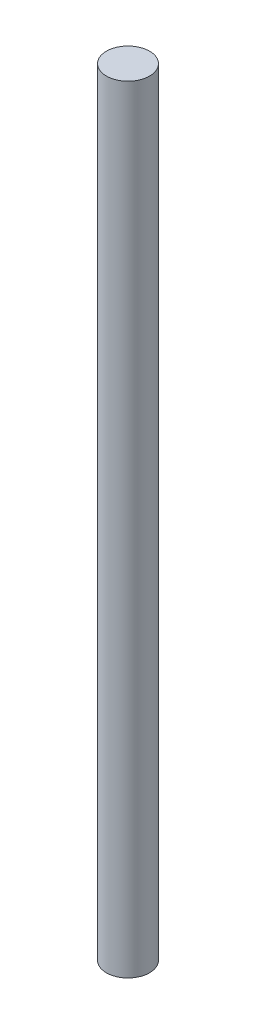
SolidWorks part; units mm, degrees
ref_plane "Front Plane" through (0, 0, 0) normal (0, 0, 1) x (1, 0, 0)
ref_plane "Top Plane" through (0, 0, 0) normal (0, 1, 0) x (1, 0, 0)
ref_plane "Right Plane" through (0, 0, 0) normal (1, 0, 0) x (0, 0, -1)
sketch "Sketch1" plane through (0, 0, 0) normal (0, 1, 0) x (1, 0, 0)
  circle A0 centre (0, 0) radius 2.5
extrude "Boss-Extrude1" add sketch "Sketch1" along normal blind 90
